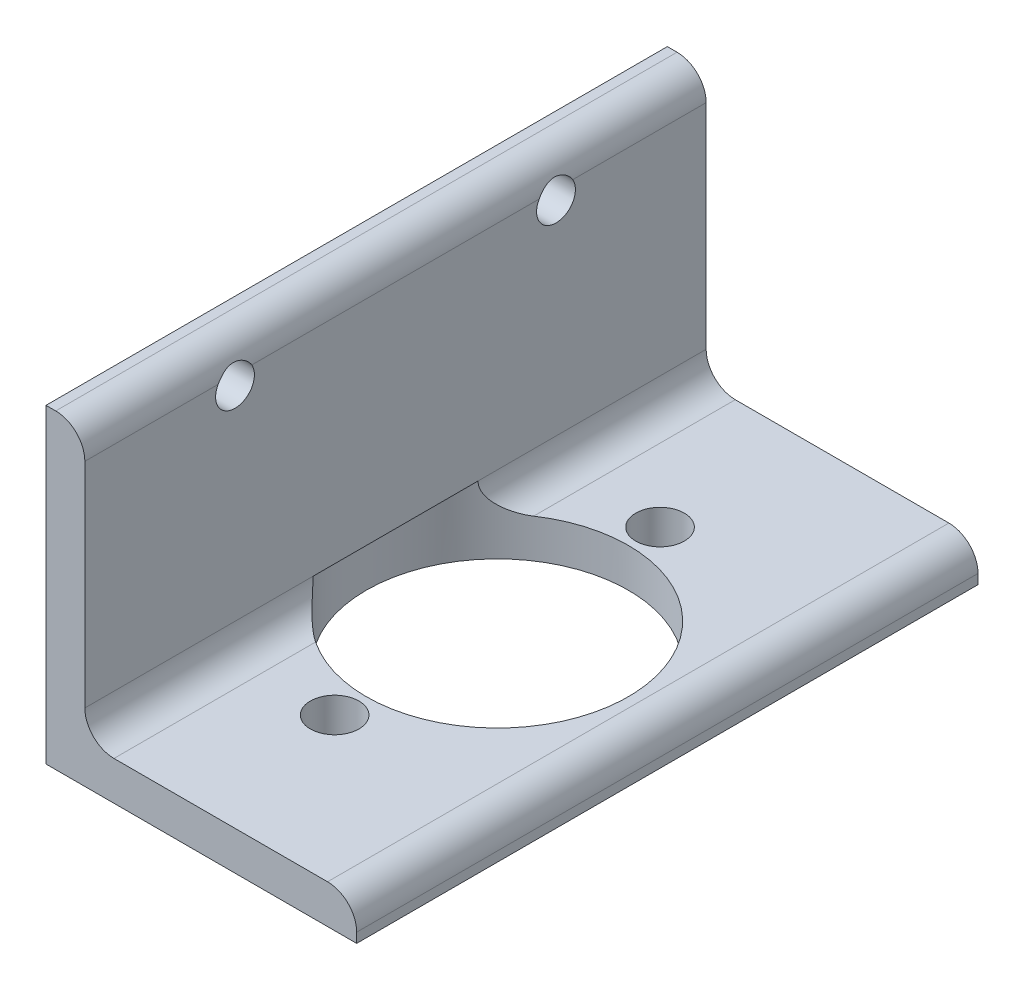
SolidWorks part; units mm, degrees
ref_plane "Front Plane" through (0, 0, 0) normal (0, 0, 1) x (1, 0, 0)
ref_plane "Top Plane" through (0, 0, 0) normal (0, 1, 0) x (1, 0, 0)
ref_plane "Right Plane" through (0, 0, 0) normal (1, 0, 0) x (0, 0, -1)
sketch "Sketch1" plane through (0, 0, 0) normal (0, 0, 1) x (1, 0, 0)
  line L0 (0, 0) -> (0, 101.6)
  line L1 (0, 101.6) -> (3.1801, 101.6)
  line L2 (12.7, 92.0801) -> (12.7, 22.225)
  line L3 (22.225, 12.7) -> (92.0801, 12.7)
  line L4 (101.6, 3.1801) -> (101.6, 0)
  line L5 (101.6, 0) -> (0, 0)
  arc A0 (101.6, 3.1801) -> (92.0801, 12.7) centre (92.0801, 3.1801) ccw
  arc A1 (3.1801, 101.6) -> (12.7, 92.0801) centre (3.1801, 92.0801) cw
  arc A2 (22.225, 12.7) -> (12.7, 22.225) centre (22.225, 22.225) cw
  circle A3 centre (0, 0) radius 9.525 construction
  dimension "D2" = 3.1801
  dimension "Radius_1" = 9.525
  dimension "Radius_2" = 9.525
  dimension "D1" = 12.7
  dimension "V_leg" = 101.6
  dimension "H_leg" = 101.6
  dimension "Thickness" = 12.7
  dimension "Flat_wid" = 3.1801
extrude "Boss-Extrude1" add sketch "Sketch1" along normal mid plane 203.2
sketch "Sketch2" plane through (0, 12.7, 0) normal (0, 1, 0) x (1, 0, 0)
  line L0 (92.0801, 0) -> (22.225, 0) construction
  line L1 (92.0801, -101.6) -> (92.0801, 101.6) construction
  line L2 (22.225, -101.6) -> (22.225, 101.6) construction
  line L3 (45.9994, 101.6) -> (45.9994, -101.6) construction
  line L6 (12.7, -101.6) -> (12.7, 101.6) construction
  circle A0 centre (45.9994, 53.213) radius 7.9375
  circle A1 centre (45.9994, -53.213) radius 7.9375
  circle A2 centre (45.9994, 0) radius 42.8625
  dimension "D1" = 53.213
  dimension "D2" = 15.875
  dimension "D3" = 85.725
  dimension "D4" = 33.2994
extrude "Cut-Extrude1" cut sketch "Sketch2" against normal up to surface (12.7 mm away) and the other way up to vertex (9.525 mm away) up to face at (50.8, 0, 0)
sketch "Sketch3" plane through (12.7, 0, 0) normal (1, 0, 0) x (0, 0, -1)
  line L1 (-101.6, 92.0801) -> (101.6, 92.0801) construction
  line L2 (-101.6, 0) -> (101.6, 0) construction
  line L3 (52.4891, 88.9) -> (-52.4891, 88.9) construction
  line L4 (0, 88.9) -> (0, 92.0801) construction
  circle A0 centre (52.4891, 88.9) radius 6.35
  circle A1 centre (-52.4891, 88.9) radius 6.35
  dimension "D2" = 12.7
  dimension "D1" = 104.9782
  dimension "D3" = 88.9
extrude "Cut-Extrude2" cut sketch "Sketch3" against normal up to next
